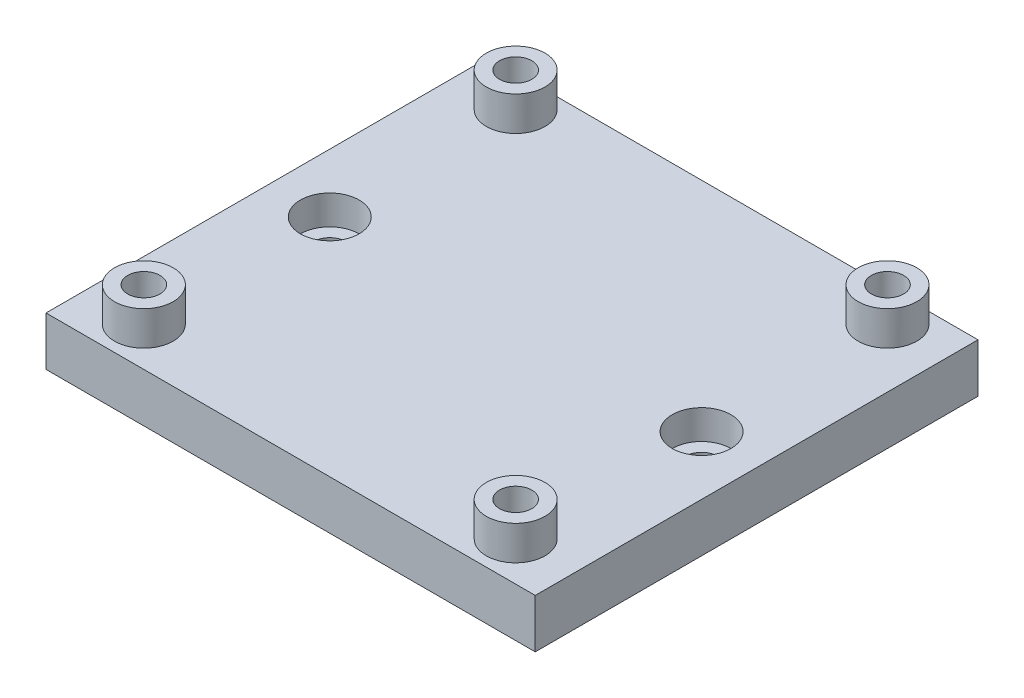
SolidWorks part; units mm, degrees
ref_plane "Front Plane" through (0, 0, 0) normal (0, 0, 1) x (1, 0, 0)
ref_plane "Top Plane" through (0, 0, 0) normal (0, 1, 0) x (1, 0, 0)
ref_plane "Right Plane" through (0, 0, 0) normal (1, 0, 0) x (0, 0, -1)
sketch "Sketch2" plane through (0, 0, 0) normal (0, 1, 0) x (1, 0, 0)
  line L0 (6, 10) -> (44, 10) construction
  line L1 (0, 0) -> (50, 0)
  line L2 (0, 0) -> (0, 55)
  line L3 (0, 55) -> (50, 55)
  line L4 (50, 0) -> (50, 55)
  line L5 (25, 10) -> (25, 48) construction
  line L6 (6, 48) -> (44, 48) construction
  line L7 (6, 29) -> (44, 29) construction
  circle A0 centre (6, 10) radius 1.65
  circle A1 centre (44, 10) radius 1.65
  circle A2 centre (44, 48) radius 1.65
  circle A3 centre (6, 48) radius 1.65
  circle A4 centre (6, 29) radius 1.65
  circle A5 centre (44, 29) radius 1.65
  point P12 (25, 48)
  point P14 (25, 0)
  point P19 (25, 29)
  dimension "D3" = 38
  dimension "D4" = 3.3
  dimension "D5" = 38
  dimension "D1" = 50
  dimension "D2" = 55
  dimension "D6" = 10
extrude "Boss-Extrude2" add sketch "Sketch2" along normal blind 6
sketch "Sketch4" plane through (0, 6, 0) normal (0, 1, 0) x (1, 0, 0)
  circle A0 centre (6, 10) radius 3
  circle A1 centre (44, 10) radius 3
  circle A2 centre (6, 48) radius 3
  circle A3 centre (44, 48) radius 3
  circle A4 centre (6, 48) radius 1.65
  circle A5 centre (44, 48) radius 1.65
  circle A6 centre (44, 10) radius 1.65
  circle A7 centre (6, 10) radius 1.65
  dimension "D1" = 6
extrude "Boss-Extrude3" add sketch "Sketch4" along normal blind 3.5
sketch "Sketch5" plane through (0, 6, 0) normal (0, 1, 0) x (1, 0, 0)
  circle A0 centre (6, 29) radius 3
  circle A1 centre (44, 29) radius 3
  dimension "D1" = 6
extrude "Cut-Extrude2" cut sketch "Sketch5" against normal blind 3
sketch "Sketch6" plane through (0, 6, 0) normal (0, 1, 0) x (1, 0, 0)
  line L0 (50, 0) -> (50, 55) construction
  line L1 (0, 55) -> (50, 55)
  line L2 (0, 55) -> (0, 51.25)
  line L3 (0, 51.25) -> (50, 51.25)
  line L4 (50, 55) -> (50, 51.25)
  line L6 (0, 0) -> (50, 0)
  line L7 (0, 0) -> (0, 6)
  line L8 (0, 6) -> (50, 6)
  line L9 (50, 0) -> (50, 6)
  dimension "D1" = 3.75
  dimension "D2" = 6
extrude "Cut-Extrude3" cut sketch "Sketch6" against normal blind 10
sketch "Sketch7" plane through (0, 0, 0) normal (0, -1, 0) x (1, 0, 0)
  line L1 (0, -6) -> (50, -6)
  line L2 (0, -6) -> (0, -51.25)
  line L3 (0, -51.25) -> (50, -51.25)
  line L4 (50, -6) -> (50, -51.25)
extrude "Cut-Extrude4" cut sketch "Sketch7" against normal blind 1
